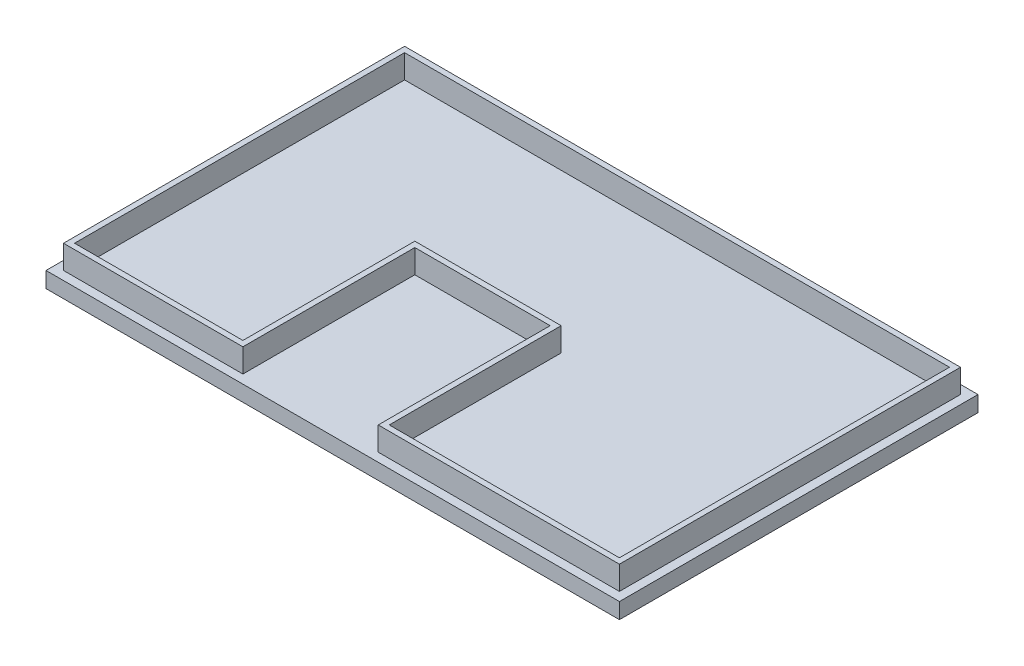
SolidWorks part; units mm, degrees
ref_plane "Front" through (0, 0, 0) normal (0, 0, 1) x (1, 0, 0)
ref_plane "Top" through (0, 0, 0) normal (0, 1, 0) x (1, 0, 0)
ref_plane "Right" through (0, 0, 0) normal (1, 0, 0) x (0, 0, -1)
sketch "Sketch1" plane through (0, 0, 0) normal (0, 1, 0) x (1, 0, 0)
  line L1 (0, 0) -> (185.1152, 0)
  line L2 (0, 0) -> (0, 115.7478)
  line L3 (0, 115.7478) -> (185.1152, 115.7478)
  line L4 (185.1152, 0) -> (185.1152, 115.7478)
  dimension "D1" = 185.1152
  dimension "D2" = 115.7478
extrude "Boss-Extrude1" add sketch "Sketch1" along normal blind 5.08 contours L2 L3 L4 L1
sketch "Sketch2" plane through (0, 5.08, 0) normal (0, 1, 0) x (1, 0, 0)
  line L0 (0, 0) -> (0, 115.7478) construction
  line L1 (2.8321, 112.9284) -> (182.2831, 112.9284)
  line L2 (2.8321, 112.9284) -> (2.8321, 2.8194)
  line L3 (60.7441, 58.3184) -> (60.7441, 2.8194)
  line L4 (182.2831, 112.9284) -> (182.2831, 2.8194)
  line L5 (0, 115.7478) -> (185.1152, 115.7478) construction
  line L7 (60.7441, 58.3184) -> (104.4321, 58.3184)
  line L8 (60.7441, 2.8194) -> (2.8321, 2.8194)
  line L9 (2.8321, 2.8194) -> (2.9314, 3.2122)
  line L11 (104.4321, 58.3184) -> (104.4321, 2.8194)
  line L12 (104.4321, 2.8194) -> (182.2831, 2.8194)
  line L14 (4.6101, 111.1504) -> (4.6101, 4.5974)
  line L15 (4.6101, 4.5974) -> (58.9661, 4.5974)
  line L16 (58.9661, 4.5974) -> (58.9661, 60.0964)
  line L17 (58.9661, 60.0964) -> (106.2101, 60.0964)
  line L18 (106.2101, 60.0964) -> (106.2101, 4.5974)
  line L19 (106.2101, 4.5974) -> (180.5051, 4.5974)
  line L20 (180.5051, 4.5974) -> (180.5051, 111.1504)
  line L21 (180.5051, 111.1504) -> (4.6101, 111.1504)
  point P4 (2.8321, 57.8739)
  point P7 (0, 57.8739)
  point P8 (92.5576, 112.9284)
  point P11 (92.5576, 115.7478)
  dimension "D1" = 179.451
  dimension "D2" = 110.109
  dimension "D3" = 110.109
  dimension "D4" = 77.851
  dimension "D5" = 57.912
  dimension "D6" = 55.499
  dimension "D7" = 1.778
  dimension "D8" = 1.778
  dimension "D9" = 1.778
  dimension "D10" = 1.778
  dimension "D11" = 1.778
  dimension "D12" = 1.778
  dimension "D13" = 1.778
  dimension "D14" = 1.778
extrude "Boss-Extrude2" add sketch "Sketch2" along normal blind 7.62 contours L8 L3 L7 L11 L12 L4 L1 L2 | L14 L15 L16 L17 L18 L19 L20 L21
